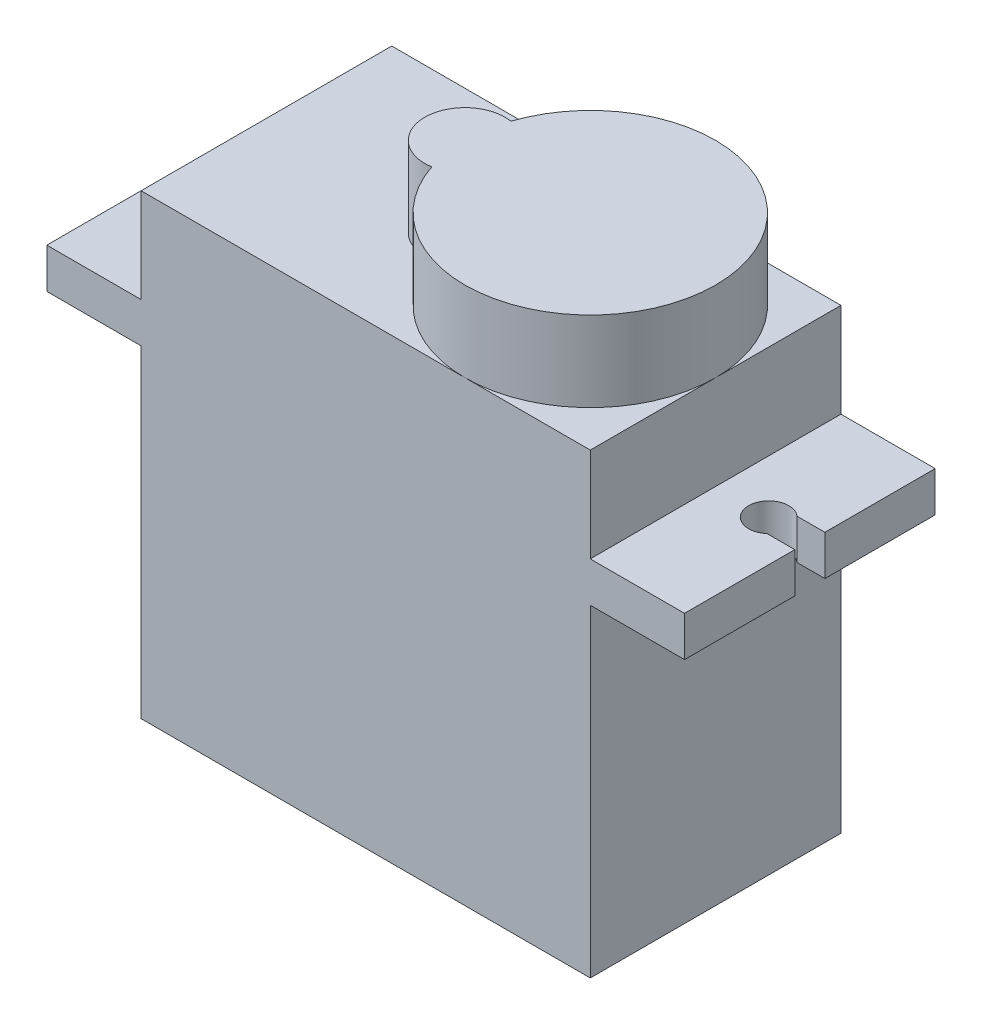
SolidWorks part; units mm, degrees
ref_plane "Plano frontal" through (0, 0, 0) normal (0, 0, 1) x (1, 0, 0)
ref_plane "Plano superior" through (0, 0, 0) normal (0, 1, 0) x (1, 0, 0)
ref_plane "Plano direito" through (0, 0, 0) normal (1, 0, 0) x (0, 0, -1)
sketch "Esboço1" plane through (0, 0, 0) normal (0, 0, 1) x (1, 0, 0)
  line L0 (11.2, -11.4) -> (11.2, 4.7) construction
  line L1 (-11.2, -11.4) -> (11.2, -11.4)
  line L2 (-11.2, -11.4) -> (-11.2, 4.7)
  line L3 (-11.2, 11.4) -> (11.2, 11.4)
  line L4 (11.2, -11.4) -> (11.2, 4.7)
  line L5 (-11.2, -11.4) -> (11.2, 11.4) construction
  line L6 (-11.2, 11.4) -> (11.2, -11.4) construction
  line L7 (11.2, 4.7) -> (15.9, 4.7)
  line L8 (15.9, 4.7) -> (15.9, 6.7)
  line L9 (15.9, 6.7) -> (11.2, 6.7)
  line L10 (0, -11.4) -> (0, 11.4) construction
  line L11 (-15.9, 4.7) -> (-15.9, 6.7)
  line L12 (-15.9, 6.7) -> (-11.2, 6.7)
  line L13 (-11.2, 4.7) -> (-15.9, 4.7)
  line L14 (-11.2, 6.7) -> (-11.2, 11.4)
  line L15 (11.2, 6.7) -> (11.2, 11.4)
  point P0 (0, 0)
  dimension "D1" = 22.8
  dimension "D2" = 22.4
  dimension "D3" = 16.1
  dimension "D4" = 31.8
  dimension "D5" = 2
extrude "Ressalto-extrusão1" add sketch "Esboço1" along normal blind 12.5
sketch "Esboço2" plane through (0, 11.4, 0) normal (0, 1, 0) x (1, 0, 0)
  line L0 (0, 0) -> (0, -12.5) construction
  line L1 (11.2, 0) -> (-11.2, 0) construction
  line L2 (11.2, -12.5) -> (-11.2, -12.5) construction
  line L3 (13.85, -6.25) -> (-13.85, -6.25) construction
  line L4 (-13.85, -6.25) -> (-15.9, -6.25) construction
  line L5 (-15.9, -12.5) -> (-15.9, 0) construction
  line L6 (-14.5114, -5.5) -> (-15.9, -5.5)
  line L7 (-14.5114, -7) -> (-15.9, -7)
  line L8 (-13.85, -7) -> (-15.9, -7) construction
  line L9 (-13.85, -5.5) -> (-15.9, -5.5) construction
  line L10 (-15.9, -5.5) -> (-15.9, -7)
  line L11 (14.5114, -7) -> (15.9, -7)
  line L12 (15.9, -5.5) -> (15.9, -7)
  line L13 (14.5114, -5.5) -> (15.9, -5.5)
  arc A0 (-14.5114, -7) -> (-14.5114, -5.5) centre (-13.85, -6.25) ccw
  circle A1 centre (13.85, -6.25) radius 1
  point P9 (0, -6.25)
  dimension "D1" = 2
  dimension "D2" = 2
  dimension "D3" = 27.7
  dimension "D4" = 0.75
  dimension "D5" = 0.75
extrude "Corte-extrusão1" cut sketch "Esboço2" against normal blind 12.5 contours L7 A0 L6 L10 | A1 | A1 L11 L12 L13
sketch "Esboço3" plane through (0, 11.4, 0) normal (0, 1, 0) x (1, 0, 0)
  line L0 (11.2, -6.25) -> (4.95, -6.25) construction
  line L1 (11.2, -12.5) -> (11.2, 0) construction
  arc A0 (-0.98, -8.2242) -> (-0.98, -4.2758) centre (4.95, -6.25) ccw
  arc A1 (-0.98, -4.2758) -> (-0.98, -8.2242) centre (-1.3, -6.25) ccw
  dimension "D2" = 4
  dimension "D1" = 6.25
extrude "Ressalto-extrusão2" add sketch "Esboço3" along normal blind 4
